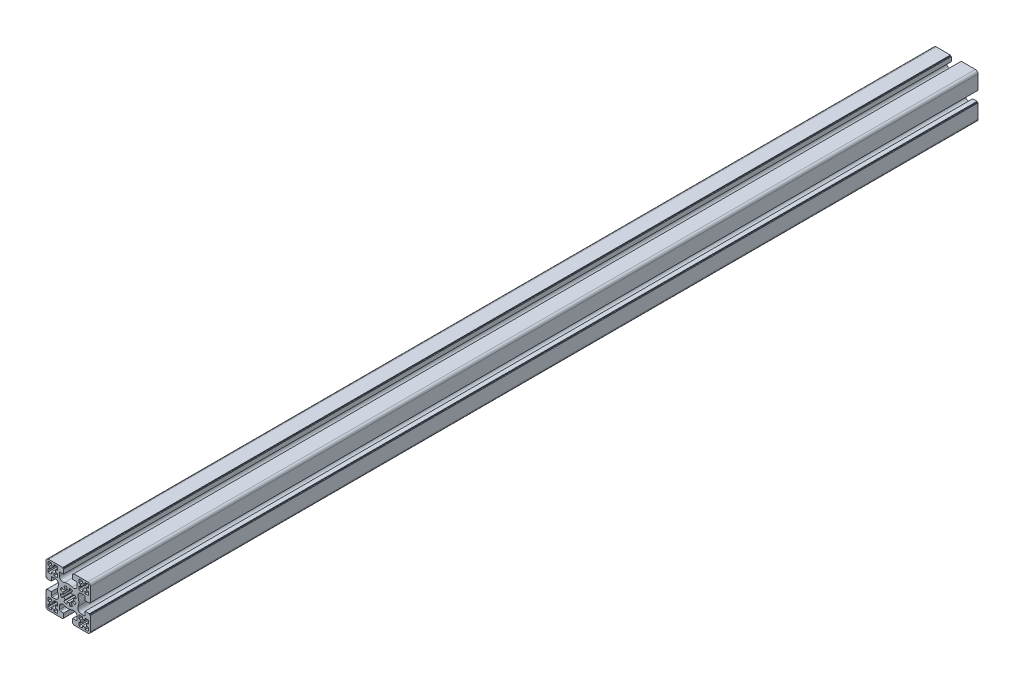
SolidWorks part; units mm, degrees
ref_plane "前视基准面" through (0, 0, 0) normal (0, 0, 1) x (1, 0, 0)
ref_plane "上视基准面" through (0, 0, 0) normal (0, 1, 0) x (1, 0, 0)
ref_plane "右视基准面" through (0, 0, 0) normal (1, 0, 0) x (0, 0, -1)
sketch "草图1" plane through (0, 0, 0) normal (0, 0, 1) x (1, 0, 0)
  line L0 (20.6121, 47.5184) -> (17.6698, 46.9331)
  line L1 (17.6698, 50.4448) -> (20.6121, 49.8595)
  line L2 (21.508, 52.0224) -> (19.0136, 53.6891)
  line L3 (21.4967, 56.1722) -> (23.1634, 53.6778)
  line L4 (25.3263, 54.5737) -> (24.741, 57.516)
  line L5 (28.2527, 57.516) -> (27.6674, 54.5737)
  line L6 (16.4969, 66.689) -> (16.4969, 63.5214)
  line L7 (21.3969, 67.689) -> (17.4969, 67.689)
  line L8 (21.3969, 72.689) -> (21.3969, 67.689)
  line L9 (20.3969, 72.689) -> (21.3969, 72.689)
  line L10 (20.3969, 73.689) -> (20.3969, 72.689)
  line L11 (4.4969, 73.689) -> (20.3969, 73.689)
  line L12 (1.4969, 54.789) -> (1.4969, 70.689)
  line L13 (2.4969, 54.789) -> (1.4969, 54.789)
  line L14 (2.4969, 53.789) -> (2.4969, 54.789)
  line L15 (7.4969, 53.789) -> (2.4969, 53.789)
  line L16 (7.4969, 57.689) -> (7.4969, 53.789)
  line L17 (11.6645, 58.689) -> (8.4969, 58.689)
  line L18 (8.4969, 38.689) -> (11.6645, 38.689)
  line L19 (7.4969, 43.589) -> (7.4969, 39.689)
  line L20 (2.4969, 43.589) -> (7.4969, 43.589)
  line L21 (2.4969, 42.589) -> (2.4969, 43.589)
  line L22 (1.4969, 42.589) -> (2.4969, 42.589)
  line L23 (1.4969, 26.689) -> (1.4969, 42.589)
  line L24 (20.3969, 23.689) -> (4.4969, 23.689)
  line L25 (20.3969, 24.689) -> (20.3969, 23.689)
  line L26 (21.3969, 24.689) -> (20.3969, 24.689)
  line L27 (21.3969, 29.689) -> (21.3969, 24.689)
  line L28 (17.4969, 29.689) -> (21.3969, 29.689)
  line L29 (16.4969, 33.8566) -> (16.4969, 30.689)
  line L30 (36.4969, 30.689) -> (36.4969, 33.8566)
  line L31 (31.5969, 29.689) -> (35.4969, 29.689)
  line L32 (31.5969, 24.689) -> (31.5969, 29.689)
  line L33 (32.5969, 24.689) -> (31.5969, 24.689)
  line L34 (32.5969, 23.689) -> (32.5969, 24.689)
  line L35 (48.4969, 23.689) -> (32.5969, 23.689)
  line L36 (51.4969, 42.589) -> (51.4969, 26.689)
  line L37 (50.4969, 42.589) -> (51.4969, 42.589)
  line L38 (50.4969, 43.589) -> (50.4969, 42.589)
  line L39 (45.4969, 43.589) -> (50.4969, 43.589)
  line L40 (45.4969, 39.689) -> (45.4969, 43.589)
  line L41 (41.3293, 38.689) -> (44.4969, 38.689)
  line L42 (44.4969, 58.689) -> (41.3293, 58.689)
  line L43 (45.4969, 53.789) -> (45.4969, 57.689)
  line L44 (50.4969, 53.789) -> (45.4969, 53.789)
  line L45 (50.4969, 54.789) -> (50.4969, 53.789)
  line L46 (51.4969, 54.789) -> (50.4969, 54.789)
  line L47 (51.4969, 70.689) -> (51.4969, 54.789)
  line L48 (32.5969, 73.689) -> (48.4969, 73.689)
  line L49 (32.5969, 72.689) -> (32.5969, 73.689)
  line L50 (31.5969, 72.689) -> (32.5969, 72.689)
  line L51 (31.5969, 67.689) -> (31.5969, 72.689)
  line L52 (35.4969, 67.689) -> (31.5969, 67.689)
  line L53 (36.4969, 63.5214) -> (36.4969, 66.689)
  line L54 (3.4969, 29.689) -> (3.4969, 26.689)
  line L55 (5.5969, 29.689) -> (3.4969, 29.689)
  line L56 (5.5969, 32.689) -> (5.5969, 29.689)
  line L57 (3.4969, 32.689) -> (5.5969, 32.689)
  line L58 (3.4969, 36.689) -> (3.4969, 32.689)
  line L59 (7.4969, 36.689) -> (3.4969, 36.689)
  line L60 (7.4969, 34.589) -> (7.4969, 36.689)
  line L61 (10.4969, 34.589) -> (7.4969, 34.589)
  line L62 (10.4969, 36.689) -> (10.4969, 34.589)
  line L63 (13.4969, 36.689) -> (10.4969, 36.689)
  line L64 (14.4969, 32.689) -> (14.4969, 35.689)
  line L65 (12.3969, 32.689) -> (14.4969, 32.689)
  line L66 (12.3969, 29.689) -> (12.3969, 32.689)
  line L67 (14.4969, 29.689) -> (12.3969, 29.689)
  line L68 (14.4969, 25.689) -> (14.4969, 29.689)
  line L69 (10.4969, 25.689) -> (14.4969, 25.689)
  line L70 (10.4969, 27.789) -> (10.4969, 25.689)
  line L71 (7.4969, 27.789) -> (10.4969, 27.789)
  line L72 (7.4969, 25.689) -> (7.4969, 27.789)
  line L73 (4.4969, 25.689) -> (7.4969, 25.689)
  line L74 (45.4969, 25.689) -> (48.4969, 25.689)
  line L75 (45.4969, 27.789) -> (45.4969, 25.689)
  line L76 (42.4969, 27.789) -> (45.4969, 27.789)
  line L77 (42.4969, 25.689) -> (42.4969, 27.789)
  line L78 (38.4969, 25.689) -> (42.4969, 25.689)
  line L79 (38.4969, 29.689) -> (38.4969, 25.689)
  line L80 (40.5969, 29.689) -> (38.4969, 29.689)
  line L81 (40.5969, 32.689) -> (40.5969, 29.689)
  line L82 (38.4969, 32.689) -> (40.5969, 32.689)
  line L83 (38.4969, 35.689) -> (38.4969, 32.689)
  line L84 (42.4969, 36.689) -> (39.4969, 36.689)
  line L85 (42.4969, 34.589) -> (42.4969, 36.689)
  line L86 (45.4969, 34.589) -> (42.4969, 34.589)
  line L87 (45.4969, 36.689) -> (45.4969, 34.589)
  line L88 (49.4969, 36.689) -> (45.4969, 36.689)
  line L89 (49.4969, 32.689) -> (49.4969, 36.689)
  line L90 (47.3969, 32.689) -> (49.4969, 32.689)
  line L91 (47.3969, 29.689) -> (47.3969, 32.689)
  line L92 (49.4969, 29.689) -> (47.3969, 29.689)
  line L93 (49.4969, 26.689) -> (49.4969, 29.689)
  line L94 (7.4969, 71.689) -> (4.4969, 71.689)
  line L95 (7.4969, 69.589) -> (7.4969, 71.689)
  line L96 (10.4969, 69.589) -> (7.4969, 69.589)
  line L97 (10.4969, 71.689) -> (10.4969, 69.589)
  line L98 (14.4969, 71.689) -> (10.4969, 71.689)
  line L99 (14.4969, 67.689) -> (14.4969, 71.689)
  line L100 (12.3969, 67.689) -> (14.4969, 67.689)
  line L101 (12.3969, 64.689) -> (12.3969, 67.689)
  line L102 (14.4969, 64.689) -> (12.3969, 64.689)
  line L103 (14.4969, 61.689) -> (14.4969, 64.689)
  line L104 (10.4969, 60.689) -> (13.4969, 60.689)
  line L105 (10.4969, 62.789) -> (10.4969, 60.689)
  line L106 (7.4969, 62.789) -> (10.4969, 62.789)
  line L107 (7.4969, 60.689) -> (7.4969, 62.789)
  line L108 (3.4969, 60.689) -> (7.4969, 60.689)
  line L109 (3.4969, 64.689) -> (3.4969, 60.689)
  line L110 (5.5969, 64.689) -> (3.4969, 64.689)
  line L111 (5.5969, 67.689) -> (5.5969, 64.689)
  line L112 (3.4969, 67.689) -> (5.5969, 67.689)
  line L113 (3.4969, 70.689) -> (3.4969, 67.689)
  line L114 (38.4969, 64.689) -> (38.4969, 61.689)
  line L115 (40.5969, 64.689) -> (38.4969, 64.689)
  line L116 (40.5969, 67.689) -> (40.5969, 64.689)
  line L117 (38.4969, 67.689) -> (40.5969, 67.689)
  line L118 (38.4969, 71.689) -> (38.4969, 67.689)
  line L119 (42.4969, 71.689) -> (38.4969, 71.689)
  line L120 (42.4969, 69.589) -> (42.4969, 71.689)
  line L121 (45.4969, 69.589) -> (42.4969, 69.589)
  line L122 (45.4969, 71.689) -> (45.4969, 69.589)
  line L123 (48.4969, 71.689) -> (45.4969, 71.689)
  line L124 (49.4969, 67.689) -> (49.4969, 70.689)
  line L125 (47.3969, 67.689) -> (49.4969, 67.689)
  line L126 (47.3969, 64.689) -> (47.3969, 67.689)
  line L127 (49.4969, 64.689) -> (47.3969, 64.689)
  line L128 (49.4969, 60.689) -> (49.4969, 64.689)
  line L129 (45.4969, 60.689) -> (49.4969, 60.689)
  line L130 (45.4969, 62.789) -> (45.4969, 60.689)
  line L131 (42.4969, 62.789) -> (45.4969, 62.789)
  line L132 (42.4969, 60.689) -> (42.4969, 62.789)
  line L133 (39.4969, 60.689) -> (42.4969, 60.689)
  line L134 (29.8303, 53.6778) -> (31.497, 56.1722)
  line L135 (33.9801, 53.6891) -> (31.4857, 52.0224)
  line L136 (32.3816, 49.8595) -> (35.3239, 50.4448)
  line L137 (35.3239, 46.9331) -> (32.3816, 47.5184)
  line L138 (31.4857, 45.3555) -> (33.9801, 43.6888)
  line L139 (31.497, 41.2057) -> (29.8303, 43.7001)
  line L140 (27.6674, 42.8042) -> (28.2527, 39.8619)
  line L141 (24.741, 39.8619) -> (25.3263, 42.8042)
  line L142 (23.1634, 43.7001) -> (21.4967, 41.2057)
  line L143 (19.0136, 43.6888) -> (21.508, 45.3555)
  arc A0 (3.4969, 26.689) -> (4.4969, 25.689) centre (4.4969, 26.689) ccw
  arc A1 (14.4969, 35.689) -> (13.4969, 36.689) centre (13.4969, 35.689) ccw
  arc A2 (48.4969, 25.689) -> (49.4969, 26.689) centre (48.4969, 26.689) ccw
  arc A3 (39.4969, 36.689) -> (38.4969, 35.689) centre (39.4969, 35.689) ccw
  arc A4 (4.4969, 71.689) -> (3.4969, 70.689) centre (4.4969, 70.689) ccw
  arc A5 (13.4969, 60.689) -> (14.4969, 61.689) centre (13.4969, 61.689) ccw
  arc A6 (38.4969, 61.689) -> (39.4969, 60.689) centre (39.4969, 61.689) ccw
  arc A7 (49.4969, 70.689) -> (48.4969, 71.689) centre (48.4969, 70.689) ccw
  arc A8 (31.497, 56.1722) -> (28.2527, 57.516) centre (26.4969, 48.689) ccw
  arc A9 (31.4857, 52.0224) -> (29.8303, 53.6778) centre (26.4969, 48.689) ccw
  arc A10 (35.3239, 50.4448) -> (33.9801, 53.6891) centre (26.4969, 48.689) ccw
  arc A11 (32.3816, 47.5184) -> (32.3816, 49.8595) centre (26.4969, 48.689) ccw
  arc A12 (33.9801, 43.6888) -> (35.3239, 46.9331) centre (26.4969, 48.689) ccw
  arc A13 (29.8303, 43.7001) -> (31.4857, 45.3555) centre (26.4969, 48.689) ccw
  arc A14 (28.2527, 39.8619) -> (31.497, 41.2057) centre (26.4969, 48.689) ccw
  arc A15 (25.3263, 42.8042) -> (27.6674, 42.8042) centre (26.4969, 48.689) ccw
  arc A16 (21.4967, 41.2057) -> (24.741, 39.8619) centre (26.4969, 48.689) ccw
  arc A17 (21.508, 45.3555) -> (23.1634, 43.7001) centre (26.4969, 48.689) ccw
  arc A18 (17.6698, 46.9331) -> (19.0136, 43.6888) centre (26.4969, 48.689) ccw
  arc A19 (20.6121, 49.8595) -> (20.6121, 47.5184) centre (26.4969, 48.689) ccw
  arc A20 (19.0136, 53.6891) -> (17.6698, 50.4448) centre (26.4969, 48.689) ccw
  arc A21 (23.1634, 53.6778) -> (21.508, 52.0224) centre (26.4969, 48.689) ccw
  arc A22 (24.741, 57.516) -> (21.4967, 56.1722) centre (26.4969, 48.689) ccw
  arc A23 (27.6674, 54.5737) -> (25.3263, 54.5737) centre (26.4969, 48.689) ccw
  arc A24 (30.9969, 59.8133) -> (21.9969, 59.8133) centre (26.4969, 48.689) ccw
  arc A25 (16.4969, 63.5214) -> (21.9969, 59.8133) centre (20.4969, 63.5214) ccw
  arc A26 (17.4969, 67.689) -> (16.4969, 66.689) centre (17.4969, 66.689) ccw
  arc A27 (4.4969, 73.689) -> (1.4969, 70.689) centre (4.4969, 70.689) ccw
  arc A28 (8.4969, 58.689) -> (7.4969, 57.689) centre (8.4969, 57.689) ccw
  arc A29 (15.3726, 53.189) -> (11.6645, 58.689) centre (11.6645, 54.689) ccw
  arc A30 (15.3726, 53.189) -> (15.3726, 44.189) centre (26.4969, 48.689) ccw
  arc A31 (11.6645, 38.689) -> (15.3726, 44.189) centre (11.6645, 42.689) ccw
  arc A32 (7.4969, 39.689) -> (8.4969, 38.689) centre (8.4969, 39.689) ccw
  arc A33 (1.4969, 26.689) -> (4.4969, 23.689) centre (4.4969, 26.689) ccw
  arc A34 (16.4969, 30.689) -> (17.4969, 29.689) centre (17.4969, 30.689) ccw
  arc A35 (21.9969, 37.5647) -> (16.4969, 33.8566) centre (20.4969, 33.8566) ccw
  arc A36 (21.9969, 37.5647) -> (30.9969, 37.5647) centre (26.4969, 48.689) ccw
  arc A37 (36.4969, 33.8566) -> (30.9969, 37.5647) centre (32.4969, 33.8566) ccw
  arc A38 (35.4969, 29.689) -> (36.4969, 30.689) centre (35.4969, 30.689) ccw
  arc A39 (48.4969, 23.689) -> (51.4969, 26.689) centre (48.4969, 26.689) ccw
  arc A40 (44.4969, 38.689) -> (45.4969, 39.689) centre (44.4969, 39.689) ccw
  arc A41 (37.6212, 44.189) -> (41.3293, 38.689) centre (41.3293, 42.689) ccw
  arc A42 (37.6212, 44.189) -> (37.6212, 53.189) centre (26.4969, 48.689) ccw
  arc A43 (41.3293, 58.689) -> (37.6212, 53.189) centre (41.3293, 54.689) ccw
  arc A44 (45.4969, 57.689) -> (44.4969, 58.689) centre (44.4969, 57.689) ccw
  arc A45 (51.4969, 70.689) -> (48.4969, 73.689) centre (48.4969, 70.689) ccw
  arc A46 (36.4969, 66.689) -> (35.4969, 67.689) centre (35.4969, 66.689) ccw
  arc A47 (30.9969, 59.8133) -> (36.4969, 63.5214) centre (32.4969, 63.5214) ccw
extrude "拉伸1" add sketch "草图1" along normal blind 1000
